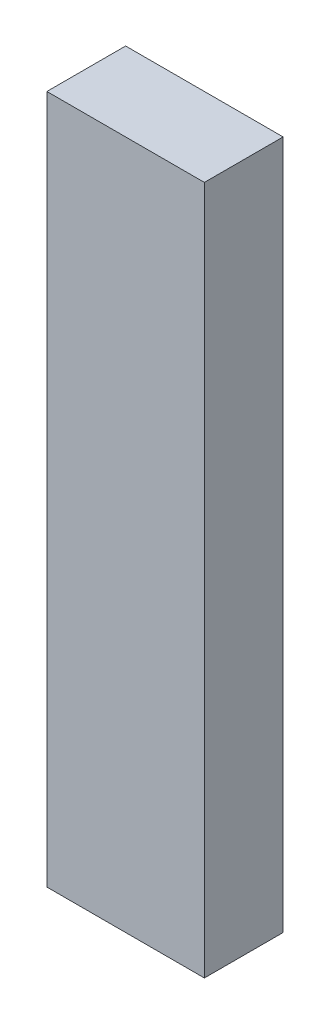
SolidWorks part; units mm, degrees
ref_plane "Front Plane" through (0, 0, 0) normal (0, 0, 1) x (1, 0, 0)
ref_plane "Top Plane" through (0, 0, 0) normal (0, 1, 0) x (1, 0, 0)
ref_plane "Right Plane" through (0, 0, 0) normal (1, 0, 0) x (0, 0, -1)
sketch "Sketch1" plane through (0, 0, 0) normal (0, 0, 1) x (1, 0, 0)
  line L1 (-4, -17.5) -> (4, -17.5)
  line L2 (-4, -17.5) -> (-4, 17.5)
  line L3 (-4, 17.5) -> (4, 17.5)
  line L4 (4, -17.5) -> (4, 17.5)
  line L5 (-4, -17.5) -> (4, 17.5) construction
  line L6 (-4, 17.5) -> (4, -17.5) construction
  point P0 (0, 0)
  dimension "D1" = 8
  dimension "D2" = 35
extrude "Boss-Extrude1" add sketch "Sketch1" along normal blind 4
